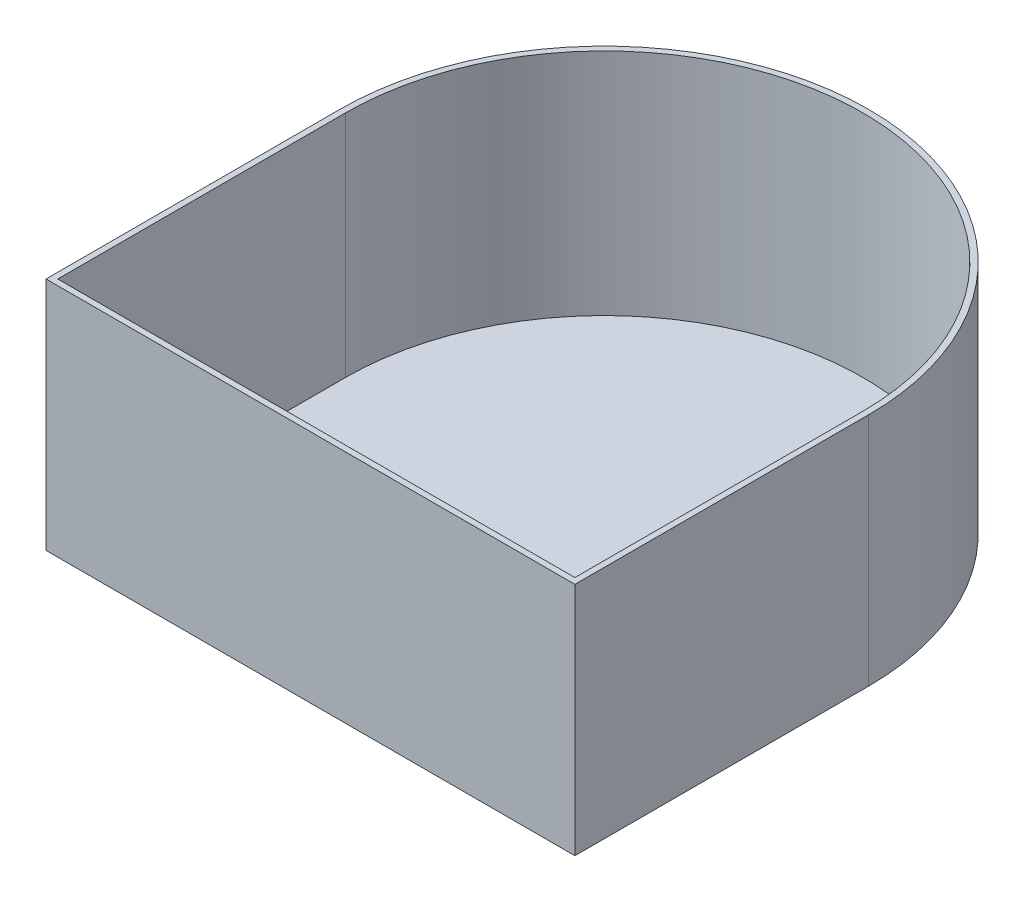
SolidWorks part; units mm, degrees
ref_plane "Front Plane" through (0, 0, 0) normal (0, 0, 1) x (1, 0, 0)
ref_plane "Top Plane" through (0, 0, 0) normal (0, 1, 0) x (1, 0, 0)
ref_plane "Right Plane" through (0, 0, 0) normal (1, 0, 0) x (0, 0, -1)
sketch "Sketch1" plane through (0, 0, 0) normal (0, 1, 0) x (1, 0, 0)
  line L0 (-45, 0) -> (-45, -50)
  line L1 (-45, -50) -> (45, -50)
  line L2 (45, -50) -> (45, 0)
  arc A0 (-45, 0) -> (45, 0) centre (0, 0) cw
  dimension "D1" = 90
  dimension "D2" = 50
extrude "Boss-Extrude1" add sketch "Sketch1" along normal blind 40
shell "Shell1" thickness 1
